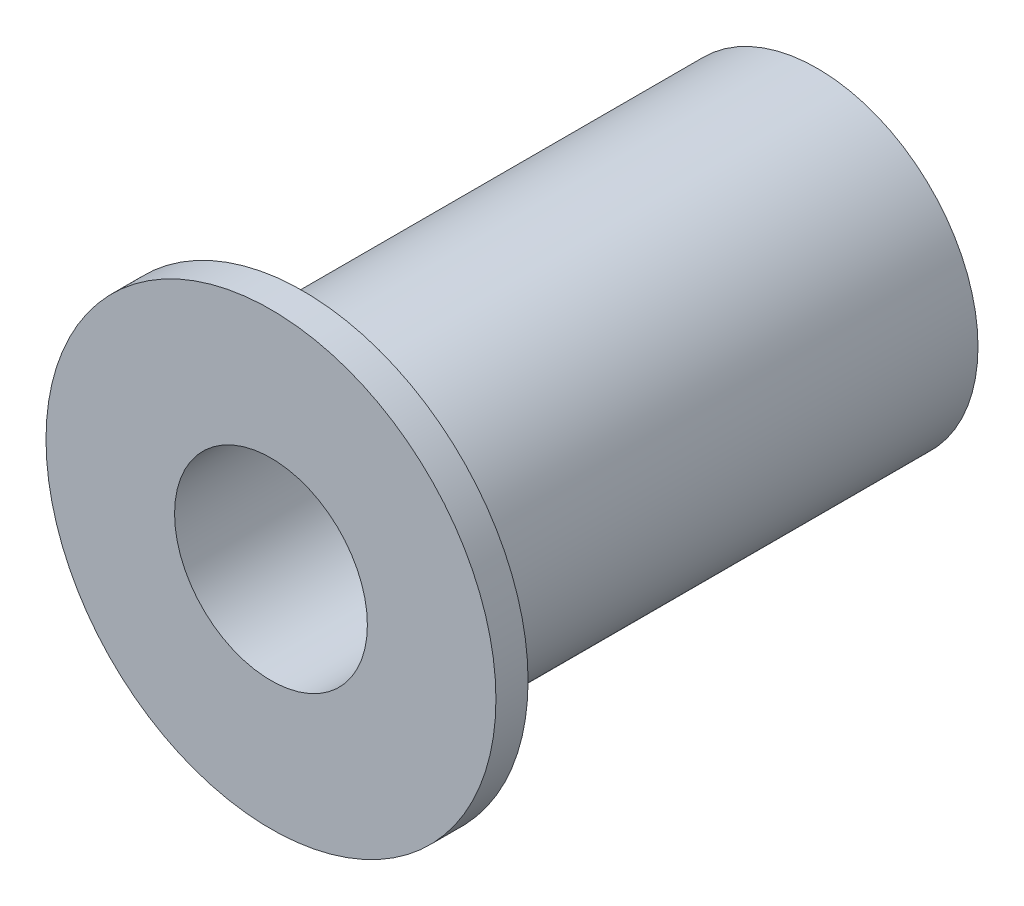
SolidWorks part; units mm, degrees
material "Aluminum Bronze"
ref_plane "Front Plane" through (0, 0, 0) normal (0, 0, 1) x (1, 0, 0)
ref_plane "Top Plane" through (0, 0, 0) normal (0, 1, 0) x (1, 0, 0)
ref_plane "Right Plane" through (0, 0, 0) normal (1, 0, 0) x (0, 0, -1)
sketch "Sketch1" plane through (0, 0, 0) normal (0, 0, 1) x (1, 0, 0)
  circle A0 centre (0, 0) radius 4.7625
  circle A1 centre (0, 0) radius 7.9375
  dimension "D1" = 15.875
  dimension "D2" = 9.525
extrude "Boss-Extrude1" add sketch "Sketch1" along normal blind 25.4
sketch "Sketch2" plane through (0, 0, 25.4) normal (0, 0, 1) x (1, 0, 0)
  circle A0 centre (0, 0) radius 4.7625 construction
  circle A1 centre (0, 0) radius 11.1125
  circle A3 centre (0, 0) radius 4.7625
  dimension "D1" = 22.225
extrude "Boss-Extrude2" add sketch "Sketch2" along normal blind 1.5875
